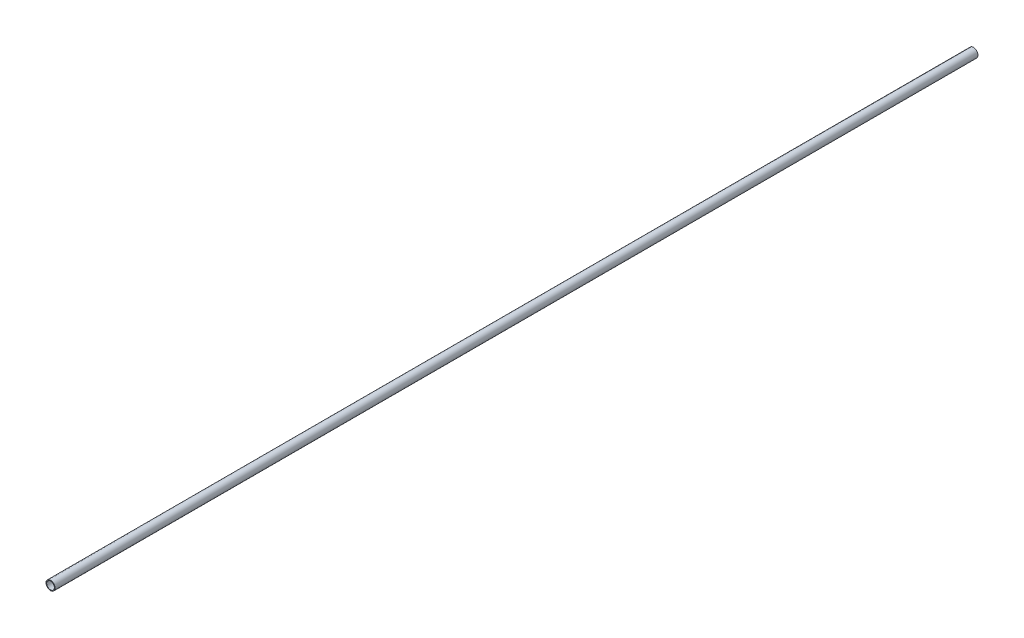
SolidWorks part; units mm, degrees
material "Hexcel AS4C (3000 Filaments)"
ref_plane "Front Plane" through (0, 0, 0) normal (0, 0, 1) x (1, 0, 0)
ref_plane "Top Plane" through (0, 0, 0) normal (0, 1, 0) x (1, 0, 0)
ref_plane "Right Plane" through (0, 0, 0) normal (1, 0, 0) x (0, 0, -1)
sketch "Sketch1" plane through (0, 0, 0) normal (0, 0, 1) x (1, 0, 0)
  circle A0 centre (0, 0) radius 4.25
  circle A1 centre (0, 0) radius 5
  dimension "D1" = 10
  dimension "D2" = 8.5
extrude "Boss-Extrude1" add sketch "Sketch1" along normal blind 1020
